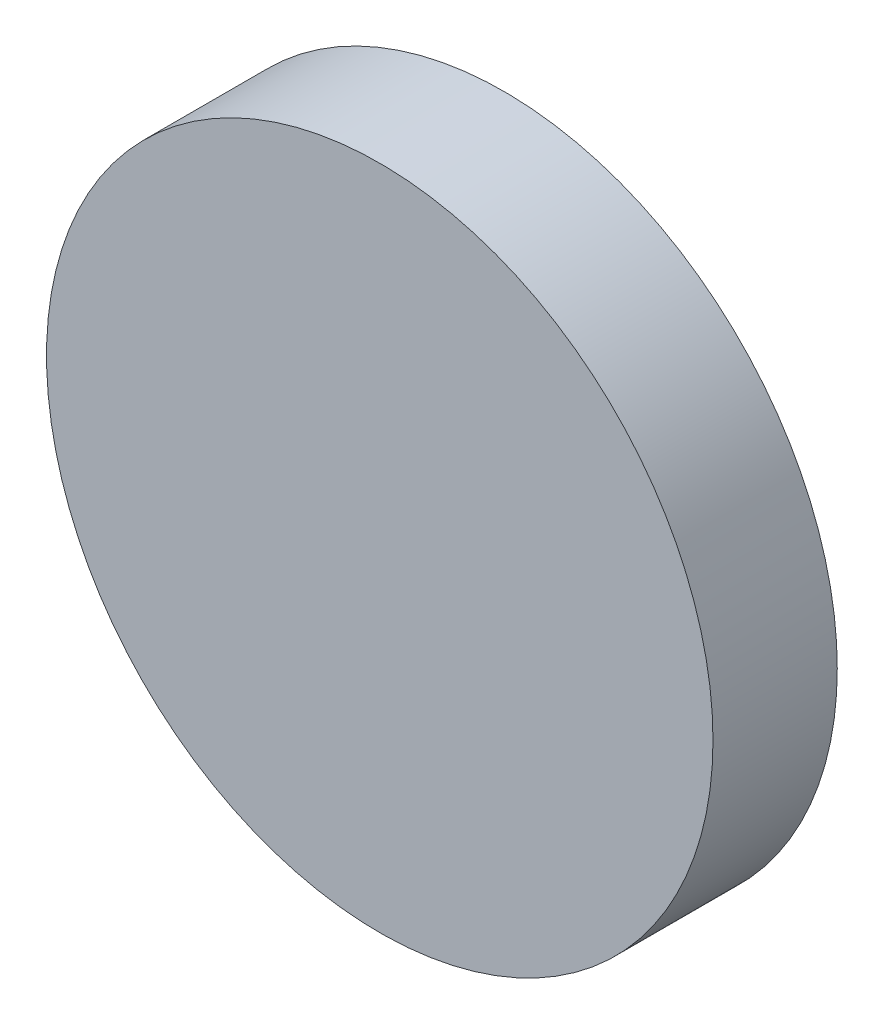
SolidWorks part; units mm, degrees
ref_plane "Front Plane" through (0, 0, 0) normal (0, 0, 1) x (1, 0, 0)
ref_plane "Top Plane" through (0, 0, 0) normal (0, 1, 0) x (1, 0, 0)
ref_plane "Right Plane" through (0, 0, 0) normal (1, 0, 0) x (0, 0, -1)
sketch "Sketch1" plane through (0, 0, 0) normal (0, 0, 1) x (1, 0, 0)
  circle A0 centre (0, 0) radius 39.95
  dimension "D1" = 79.9
extrude "Boss-Extrude1" add sketch "Sketch1" along normal blind 14.9
